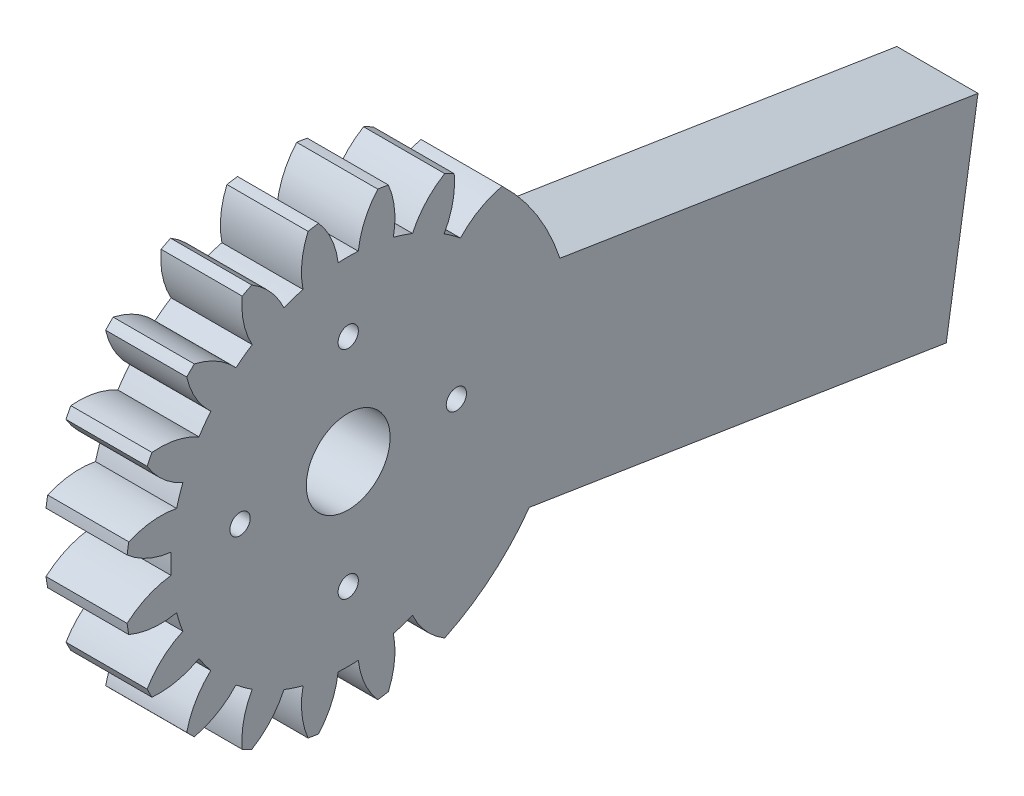
SolidWorks part; units mm, degrees
ref_plane "Plane1" through (0, 0, 0) normal (0, 0, 1) x (1, 0, 0)
ref_plane "Plane2" through (0, 0, 0) normal (0, 1, 0) x (1, 0, 0)
ref_plane "Plane3" through (0, 0, 0) normal (1, 0, 0) x (0, 0, -1)
sketch "HoldingSke" plane through (0, 0, 0) normal (0, 1, 0) x (1, 0, 0)
  line L0 (0, 0) -> (0.6265, -0.228)
  line L1 (-15, 0) -> (100, 0) construction
  line L2 (0, 0) -> (-2.1039, 2.3779)
  line L3 (0, 0) -> (-11.863, 4.5341)
  line L4 (0, 0) -> (8.1152, 2.9537)
  line L5 (0, 0) -> (-46.8476, -17.4728)
  line L6 (0, 0) -> (-4.9738, -3.3558)
  line L7 (-2.1039, 2.3779) -> (8.6586, 51.2059)
  line L8 (-76.2, 54.61) -> (-74.4, 54.61)
  line L9 (-71.009, 38.7566) -> (-53.1078, 45.2721)
  line L10 (-76.2, 71.12) -> (104.1128, 71.12)
  line L11 (0, 0) -> (-6, 0)
  line L12 (-76.2, 101.6) -> (-76.147, 101.6)
  line L13 (24.9733, 27.94) -> (52.9518, 28.4284)
  line L14 (24.9733, 27.94) -> (24.9743, 27.94)
  line L15 (24.9733, 27.94) -> (100.4006, 29.5858)
  line L16 (-63.627, -1.5) -> (-12.827, -1.5)
  circle A0 centre (0, 0) radius 5
  circle A1 centre (0, 0) radius 13.124
  circle A2 centre (0, 0) radius 37.5
  circle A3 centre (0, 0) radius 5
  dimension "MHD" = 26.248
  dimension "Hub_dia" = 75
  dimension "Bore" = 10
  dimension "MBD" = 10
  dimension "Num_teeth" = 20
  dimension "Pitch" = 0.6667
  dimension "Overall_len" = 50
  dimension "Show_teeth" = 20
  dimension "Thickness" = 6
  dimension "OAL" = 50.0001
  dimension "T_dim" = 1.8
  dimension "Ap" = 20
  dimension "H" = 19.05
  dimension "Pitch_radius" = 180.3128
  dimension "Width" = 6
  dimension "Backlash" = 0.053
  dimension "Addendum_fac" = 1
  dimension "Dedendum_fac" = 1.25
  dimension "Clearance_fac" = 0.25
  dimension "Dedendum_add" = 0.001
  dimension "Module" = 1.5
sketch "BasProSke" plane through (0, 0, 0) normal (0, 1, 0) x (1, 0, 0)
  line L0 (-10, 0) -> (60, 0) construction
  line L1 (0, 0) -> (0, 16.5)
  line L2 (0, 0) -> (6, 0)
  line L3 (6, 0) -> (6, 16.5)
  line L4 (6, 16.5) -> (0, 16.5)
  dimension "Thickness" = 6
  dimension "Diameter" = 33
revolve "Base-Revolve" add sketch "BasProSke" angle 360 about L0
sketch "TooCutSke" plane through (0, 0, 0) normal (1, 0, 0) x (0, 0, -1)
  line L1 (0, 0) -> (0, 107) construction
  line L2 (0, 0) -> (-1.2696, 14.9462) construction
  line L3 (0, 0) -> (-4.6808, 29.5532) construction
  line L4 (-1.2696, 14.9462) -> (-2.3404, 14.7766) construction
  arc A0 (0.7438, 13.1029) -> (-0.7438, 13.1029) centre (0, 0) ccw
  arc A1 (2.21, 16.377) -> (-2.21, 16.377) centre (0, 0) ccw
  circle A2 centre (0, 0) radius 15 construction
  circle A3 centre (0, 0) radius 14.0954 construction
  arc A4 (-0.7438, 13.1029) -> (-2.21, 16.377) centre (-6.7025, 12.3999) ccw
  arc A5 (2.21, 16.377) -> (0.7438, 13.1029) centre (6.7025, 12.3999) ccw
  dimension "Root_dia" = 26.248
  dimension "Overcut_dia" = 33.0508
  dimension "Pitch_dia" = 30
  dimension "Base_dia" = 28.1908
  dimension "Flank_rad" = 6
  dimension "Half_ang" = 9
  dimension "Half_CT" = 1.0841
extrude "ToothCut" cut sketch "TooCutSke" along normal through all
fillet "Breaks" [suppressed] radius 0.03
fillet "RootFillets" [suppressed] radius 0.376
pattern_circular "TeethCuts" count 20 every 18 about axis through (-10, 0, 0) along (1, 0, 0) skipping 12, 13, 14, 15, 16, 17 of "ToothCut", "RootFillets", "Breaks"
sketch "HubNeaOneSke" plane through (0, 0, 0) normal (-1, 0, 0) x (0, 0, 1)
  circle A0 centre (0, 0) radius 13.124
  dimension "Diameter" = 26.248
extrude "HubNearOne" [suppressed] add sketch "HubNeaOneSke" along normal blind 44.0001
sketch "HubNeaBotSke" plane through (0, 0, 0) normal (-1, 0, 0) x (0, 0, 1)
  circle A0 centre (0, 0) radius 13.124
  dimension "Diameter" = 26.248
extrude "HubNearBoth" [suppressed] add sketch "HubNeaBotSke" along normal blind 22
ref_plane "FarPln" through (6, 0, 0) normal (1, 0, 0) x (0, 0, -1)
sketch "HubFarSke" plane through (6, 0, 0) normal (1, 0, 0) x (0, 0, -1)
  circle A0 centre (0, 0) radius 13.124
  dimension "Diameter" = 26.248
extrude "HubFar" [suppressed] add sketch "HubFarSke" along normal blind 22
sketch "BorSke" plane through (0, 0, 0) normal (1, 0, 0) x (0, 0, -1)
  circle A0 centre (0, 0) radius 3.1
  dimension "Diameter" = 6.2
extrude "Bore" cut sketch "BorSke" along normal mid plane 100.0001
sketch "KeySke" plane through (0, 0, 0) normal (1, 0, 0) x (0, 0, -1)
  line L0 (-2, 0) -> (-2, 6.8)
  line L1 (-2, 6.8) -> (2, 6.8)
  line L2 (2, 6.8) -> (2, 0)
  line L3 (0, 0) -> (0, 34) construction
  line L4 (-2, 0) -> (2, 0)
  dimension "Offset" = 6.8
  dimension "Width" = 4
extrude "Keyway" [suppressed] cut sketch "KeySke" along normal mid plane 100.0001
pattern_circular "Keyway2" [suppressed] count 2 every 90 about axis through (-10, 0, 0) along (1, 0, 0)
sketch "Esquisse2" plane through (6, 0, 0) normal (1, 0, 0) x (0, 0, -1)
  line L0 (10.4456, 6.0174) -> (8.0991, -8.7979)
  line L1 (10.4456, 6.0174) -> (46.5851, 0.2935)
  line L2 (8.0991, -8.7979) -> (44.2386, -14.5218)
  line L3 (46.5851, 0.2935) -> (44.2386, -14.5218)
  dimension "D1" = 36.59
  dimension "D2" = 15
  dimension "D3" = 6
extrude "Boss.-Extru.1" add sketch "Esquisse2" against normal blind 6
sketch "Esquisse3" plane through (0, 0, 0) normal (-1, 0, 0) x (0, 0, 1)
  circle A0 centre (8, 0) radius 0.75
  circle A1 centre (-8, 0) radius 0.75
  circle A2 centre (0, 8) radius 0.75
  circle A3 centre (0, -8) radius 0.75
  circle A4 centre (0, 0) radius 3.1 construction
  dimension "D1" = 1.5
  dimension "D2" = 1.5
  dimension "D3" = 1.5
  dimension "D4" = 1.5
  dimension "D5" = 8
  dimension "D6" = 8
  dimension "D7" = 8
  dimension "D8" = 8
extrude "Enlèv. mat.-Extru.1" cut sketch "Esquisse3" against normal blind 6
equation "' \"Module@HoldingSke\" = 6.35"
equation "' \"Num_teeth@HoldingSke\" = 12"
equation "' \"Ap@HoldingSke\" =  20"
equation "' \"Ap@HoldingSke\" = 20"
equation "' \"Width@HoldingSke\" = 0.5 * 25.4"
equation "' \"Hub_dia@HoldingSke\"= 1 * 25.4"
equation "' \"Hub_dia@HoldingSke\" = 1 * 25.4"
equation "' \"Overall_len@HoldingSke\" = 1.0 * 25.4"
equation "' \"Bore@HoldingSke\" = 0.75 * 25.4"
equation "' \"T_dim@HoldingSke\" = 0.1 * 25.4"
equation "' \"Width@KeySke\" = 0.25 * 25.4"
equation "' \"Show_teeth@HoldingSke\" = 13"
equation "' \"Backlash@HoldingSke\" = 0.009 * 25.4"
equation "' \"Addendum_fac@HoldingSke\" = 1.0"
equation "' \"Dedendum_fac@HoldingSke\" = 1.25"
equation "' \"Dedendum_add@HoldingSke\" = 0.00005 * 25.4"
equation "' \"Clearance_fac@HoldingSke\" = 0.25"
equation "\"Pitch@HoldingSke\" = 1 / \"Module@HoldingSke\""
equation "\"Overcut_dia@TooCutSke\" = (\"Num_teeth@HoldingSke\" + 2 * \"Addendum_fac@HoldingSke\") / \"Pitch@HoldingSke\" + 0.002 * 25.4"
equation "\"Pitch_dia@TooCutSke\" = \"Num_teeth@HoldingSke\" / \"Pitch@HoldingSke\""
equation "\"Base_dia@TooCutSke\" = \"Num_teeth@HoldingSke\" / \"Pitch@HoldingSke\" * cos((\"Ap@HoldingSke\"  * 3.14159265 / 180))"
equation "\"Root_dia@TooCutSke\" = (\"Num_teeth@HoldingSke\" + 2) / \"Pitch@HoldingSke\" - 2 * (\"Addendum_fac@HoldingSke\" + \"Dedendum_fac@HoldingSke\") / \"Pitch@HoldingSke\" - \"Dedendum_add@HoldingSke\" * 2"
equation "\"Half_ang@TooCutSke\" = 180 / \"Num_teeth@HoldingSke\""
equation "\"Half_CT@TooCutSke\" = \"Num_teeth@HoldingSke\" / \"Pitch@HoldingSke\" * sin((3.14159265 / 2 / \"Num_teeth@HoldingSke\")) / 2 - 7 * \"Backlash@HoldingSke\" / 4"
equation "\"Flank_rad@TooCutSke\" = \"Num_teeth@HoldingSke\" / \"Pitch@HoldingSke\" / 5"
equation "\"Radius@RootFillets\" = \"Clearance_fac@HoldingSke\" / \"Pitch@HoldingSke\" + \"Dedendum_add@HoldingSke\""
equation "\"Break_rad@Breaks\" = 0.02 / \"Pitch@HoldingSke\""
equation "\"Thickness@HoldingSke\" = \"Width@HoldingSke\""
equation "\"OAL@HoldingSke\" = \"Thickness@HoldingSke\""
equation "\"MHD@HoldingSke\" = (\"Num_teeth@HoldingSke\" + 2) / \"Pitch@HoldingSke\" - 2 * (\"Addendum_fac@HoldingSke\" + \"Dedendum_fac@HoldingSke\")  / \"Pitch@HoldingSke\" - \"Dedendum_add@HoldingSke\" * 2"
equation "\"MBD@HoldingSke\" = (\"Num_teeth@HoldingSke\" + 2) / \"Pitch@HoldingSke\" - 2 * (\"Addendum_fac@HoldingSke\" + \"Dedendum_fac@HoldingSke\")  / \"Pitch@HoldingSke\" - \"Dedendum_add@HoldingSke\" * 2 - 0.002 * 25.4"
equation "\"MHD@HoldingSke\" = ((sgn( \"MHD@HoldingSke\" - \"Hub_dia@HoldingSke\" )-1)*( \"MHD@HoldingSke\" - \"Hub_dia@HoldingSke\" ))/-2+ \"Hub_dia@HoldingSke\""
equation "\"MBD@HoldingSke\" = ((sgn( \"MBD@HoldingSke\" - \"Bore@HoldingSke\" )-1)*( \"MBD@HoldingSke\" - \"Bore@HoldingSke\" ))/-2+ \"Bore@HoldingSke\""
equation "\"OAL@HoldingSke\" = ((sgn( \"OAL@HoldingSke\" - \"Overall_len@HoldingSke\" )+1)*( \"OAL@HoldingSke\" - \"Overall_len@HoldingSke\" ))/2 + \"Overall_len@HoldingSke\" + 0.000002 * 25.4"
equation "\"Num_teeth@TeethCuts\" = int( \"Show_teeth@HoldingSke\" ) + 1"
equation "\"Num_teeth@TeethCuts\" = ((sgn( \"Num_teeth@TeethCuts\" - \"Num_teeth@HoldingSke\" )-1)*( \"Num_teeth@TeethCuts\" - \"Num_teeth@HoldingSke\" ))/-2+ \"Num_teeth@HoldingSke\""
equation "\"Num_teeth@TeethCuts\" = ((sgn( \"Num_teeth@TeethCuts\" - 2.0)+1)*( \"Num_teeth@TeethCuts\" - 2.0))/2 +2.0"
equation "\"Angle@TeethCuts\" = 360.0 / \"Num_teeth@HoldingSke\""
equation "\"Diameter@BasProSke\" = (\"Num_teeth@HoldingSke\" + 2 * \"Addendum_fac@HoldingSke\") / \"Pitch@HoldingSke\""
equation "\"Thickness@BasProSke\"  = \"Thickness@HoldingSke\""
equation "' \"Fillet_rad@BasProSke\" =  \"Thickness@HoldingSke\" * 0.05"
equation "' \"Fillet_rad@BasProSke\" = \"Thickness@HoldingSke\" * 0.05"
equation "\"MHD@HoldingSke\" = ((sgn( \"MHD@HoldingSke\" - \"Root_dia@TooCutSke\" )-1)*( \"MHD@HoldingSke\" - \"Root_dia@TooCutSke\" ))/-2+ \"Root_dia@TooCutSke\""
equation "\"Diameter@HubNeaOneSke\" = \"MHD@HoldingSke\""
equation "\"Length@HubNearOne\" = \"OAL@HoldingSke\" - \"Thickness@BasProSke\""
equation "\"Diameter@HubNeaBotSke\" = \"MHD@HoldingSke\""
equation "\"Length@HubNearBoth\" = ( \"OAL@HoldingSke\" - \"Thickness@BasProSke\" ) / 2.0"
equation "\"Thickness@FarPln\" = \"Thickness@BasProSke\""
equation "\"Diameter@HubFarSke\" = \"MHD@HoldingSke\""
equation "\"Length@HubFar\" = ( \"OAL@HoldingSke\" - \"Thickness@BasProSke\" ) / 2.0"
equation "\"D1@Bore\" = \"OAL@HoldingSke\" * 2.0"
equation "\"D1@Keyway\" = \"OAL@HoldingSke\" * 2.0"
equation "\"Offset@KeySke\" = \"T_dim@HoldingSke\" + \"MBD@HoldingSke\" / 2.0"
